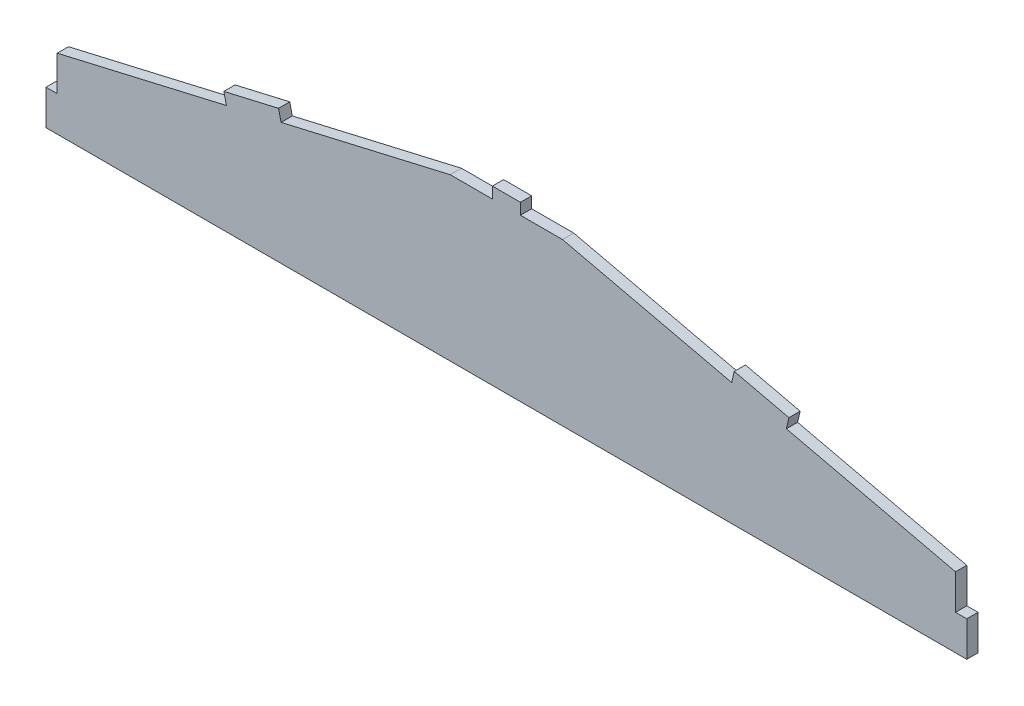
SolidWorks part; units mm, degrees
ref_plane "Front Plane" through (0, 0, 0) normal (0, 0, 1) x (1, 0, 0)
ref_plane "Top Plane" through (0, 0, 0) normal (0, 1, 0) x (1, 0, 0)
ref_plane "Right Plane" through (0, 0, 0) normal (1, 0, 0) x (0, 0, -1)
sketch "Sketch1" plane through (0, 0, 0) normal (0, 0, 1) x (1, 0, 0)
  line L0 (-203.2, 0) -> (-203.2, 31.75)
  line L1 (-203.2, 31.75) -> (-25.4, 73.025)
  line L2 (-25.4, 73.025) -> (0, 73.025)
  line L3 (0, 73.025) -> (0, 0)
  line L4 (0, 0) -> (-203.2, 0)
  dimension "D1" = 203.2
  dimension "D2" = 31.75
  dimension "D3" = 73.025
  dimension "D4" = 25.4
extrude "Boss-Extrude1" add sketch "Sketch1" along normal blind 5.08
mirror "Mirror1" about plane through (0, 73.025, 5.08) normal (-1, 0, 0) of "Boss-Extrude1"
sketch "Sketch2" plane through (0, 0, 5.08) normal (0, 0, 1) x (1, 0, 0)
  line L0 (-126.671, 49.5157) -> (-101.929, 55.2593)
  line L1 (-126.671, 49.5157) -> (-127.8198, 54.4641)
  line L2 (-101.929, 55.2593) -> (-103.0777, 60.2078)
  line L3 (-127.8198, 54.4641) -> (-103.0777, 60.2078)
  line L4 (-25.4, 73.025) -> (-203.2, 31.75) construction
  line L5 (-203.2, 0) -> (-203.2, 15.875)
  line L6 (-203.2, 0) -> (-208.28, 0)
  line L7 (-203.2, 15.875) -> (-208.28, 15.875)
  line L8 (-208.28, 0) -> (-208.28, 15.875)
  line L9 (-203.2, 31.75) -> (-203.2, 0) construction
  line L10 (-6.35, 73.025) -> (6.35, 73.025)
  line L11 (-6.35, 73.025) -> (-6.35, 78.105)
  line L12 (6.35, 73.025) -> (6.35, 78.105)
  line L13 (-6.35, 78.105) -> (6.35, 78.105)
  line L14 (25.4, 73.025) -> (-25.4, 73.025) construction
  line L15 (203.2, 0) -> (203.2, 15.875)
  line L16 (203.2, 0) -> (208.28, 0)
  line L17 (203.2, 15.875) -> (208.28, 15.875)
  line L18 (208.28, 0) -> (208.28, 15.875)
  line L19 (203.2, 31.75) -> (203.2, 0) construction
  line L20 (126.671, 49.5157) -> (101.929, 55.2593)
  line L21 (126.671, 49.5157) -> (127.8198, 54.4641)
  line L22 (101.929, 55.2593) -> (103.0777, 60.2078)
  line L23 (127.8198, 54.4641) -> (103.0777, 60.2078)
  line L24 (25.4, 73.025) -> (203.2, 31.75) construction
  point P7 (-114.3, 52.3875)
  point P8 (-114.3, 52.3875)
  point P35 (114.3, 52.3875)
  point P36 (0, 73.025)
  point P38 (0, 73.025)
  dimension "D1" = 25.4
  dimension "D2" = 5.08
  dimension "D3" = 12.7
extrude "Boss-Extrude2" add sketch "Sketch2" against normal blind 5.08
